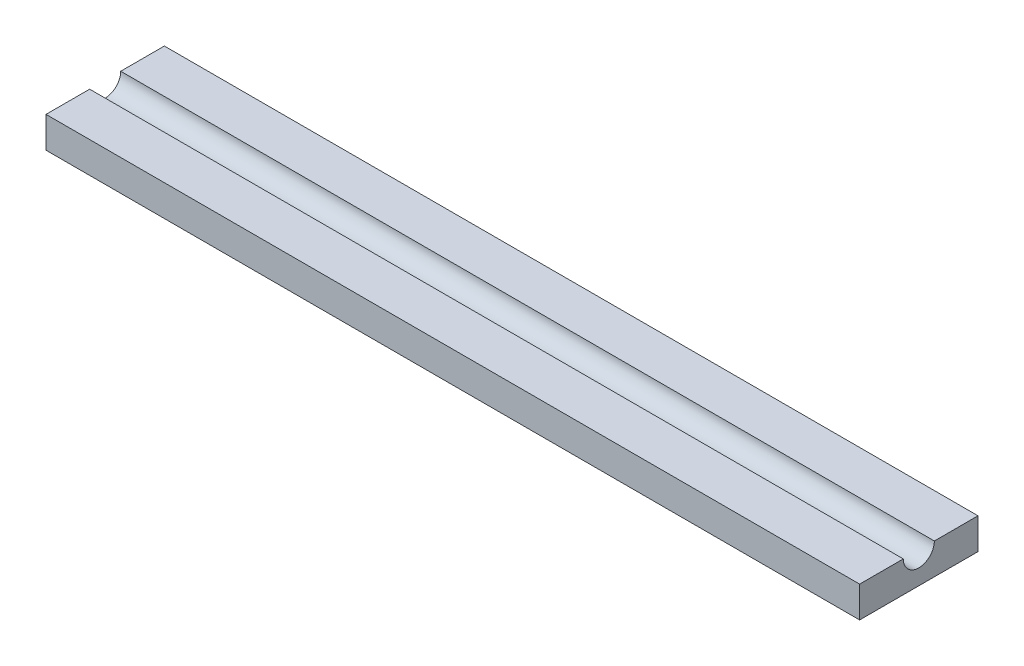
SolidWorks part; units mm, degrees
ref_plane "Front Plane" through (0, 0, 0) normal (0, 0, 1) x (1, 0, 0)
ref_plane "Top Plane" through (0, 0, 0) normal (0, 1, 0) x (1, 0, 0)
ref_plane "Right Plane" through (0, 0, 0) normal (1, 0, 0) x (0, 0, -1)
sketch "Sketch1" plane through (0, 0, 0) normal (0, 1, 0) x (1, 0, 0)
  line L1 (-81.9774, 19.6144) -> (179.9226, 19.6144)
  line L2 (-81.9774, 19.6144) -> (-81.9774, -18.4856)
  line L3 (-81.9774, -18.4856) -> (179.9226, -18.4856)
  line L4 (179.9226, 19.6144) -> (179.9226, -18.4856)
  dimension "D1" = 38.1
  dimension "D2" = 261.9
extrude "Boss-Extrude1" add sketch "Sketch1" along normal blind 10
sketch "Sketch2" plane through (179.9226, 0, 0) normal (1, 0, 0) x (0, 0, -1)
  line L1 (-18.4856, 10) -> (19.6144, 10) construction
  line L2 (-18.4856, 10) -> (-18.4856, 0) construction
  line L3 (-18.4856, 0) -> (19.6144, 0) construction
  line L4 (19.6144, 10) -> (19.6144, 0) construction
  circle A0 centre (0.5644, 10) radius 5
  point P0 (-18.4856, 10)
  point P1 (19.6144, 0)
  point P8 (0.5644, 10)
  dimension "D1" = 10
extrude "Cut-Extrude1" cut sketch "Sketch2" against normal up to surface (261.9 mm away) up to face at (-81.9774, 5, -0.5644)
